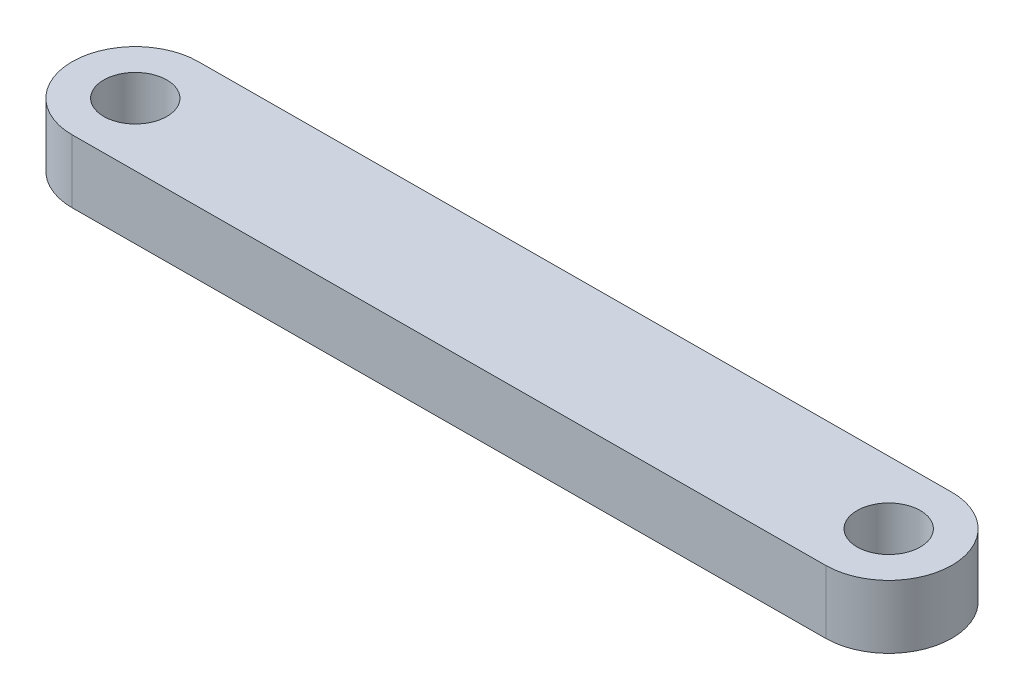
SolidWorks part; units mm, degrees
ref_plane "Front Plane" through (0, 0, 0) normal (0, 0, 1) x (1, 0, 0)
ref_plane "Top Plane" through (0, 0, 0) normal (0, 1, 0) x (1, 0, 0)
ref_plane "Right Plane" through (0, 0, 0) normal (1, 0, 0) x (0, 0, -1)
sketch "Sketch1" plane through (0, 0, 0) normal (0, 1, 0) x (1, 0, 0)
  line L0 (-32.1845, 3.2832) -> (3.3755, 3.4669)
  line L1 (-32.1845, -2.7168) -> (3.4065, -2.5329)
  circle A0 centre (-32.1845, 0.2832) radius 1.5
  circle A1 centre (3.3755, 0.4669) radius 1.5
  arc A2 (-32.1845, 3.2832) -> (-32.1535, -2.7166) centre (-32.1845, 0.2832) ccw
  arc A3 (3.3755, -2.5331) -> (3.3445, 3.4667) centre (3.3755, 0.4669) ccw
  arc A4 (-32.1535, -2.7166) -> (-32.1845, 3.2832) centre (-32.1845, 0.2832) ccw construction
  arc A5 (3.3445, 3.4667) -> (3.3755, -2.5331) centre (3.3755, 0.4669) ccw construction
  dimension "D1" = 3
  dimension "D3" = 6
  dimension "D4" = 6
  dimension "D2" = 35.56
extrude "Boss-Extrude1" add sketch "Sketch1" along normal blind 3 contours L1 A3 L0 A2 A0 A1
